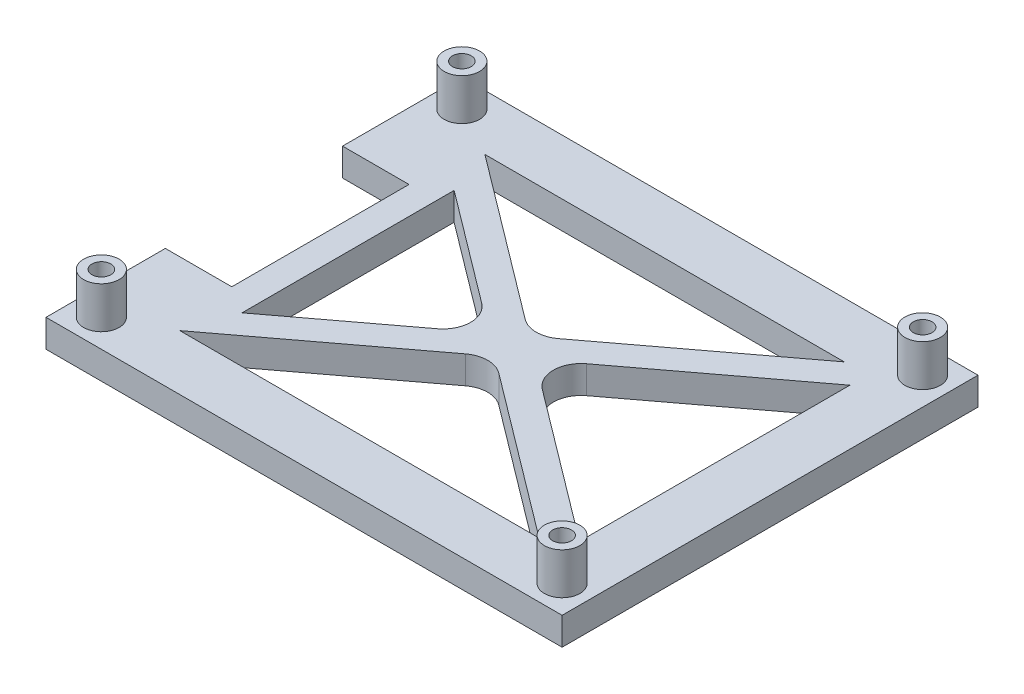
SolidWorks part; units mm, degrees
ref_plane "Front Plane" through (0, 0, 0) normal (0, 0, 1) x (1, 0, 0)
ref_plane "Top Plane" through (0, 0, 0) normal (0, 1, 0) x (1, 0, 0)
ref_plane "Right Plane" through (0, 0, 0) normal (1, 0, 0) x (0, 0, -1)
sketch "Sketch2" plane through (0, 0, 0) normal (0, 1, 0) x (1, 0, 0)
  line L0 (-36.6, -24.4209) -> (-36.6, 24.4209)
  line L1 (41.6, -32.55) -> (-41.6, -32.55) construction
  line L2 (41.6, -32.55) -> (41.6, 32.55) construction
  line L3 (41.6, 32.55) -> (-41.6, 32.55) construction
  line L4 (-41.6, -32.55) -> (-41.6, 32.55) construction
  line L5 (41.6, -32.55) -> (-41.6, 32.55) construction
  line L6 (41.6, 32.55) -> (-41.6, -32.55) construction
  line L8 (36.6, -24.4209) -> (36.6, 24.4209)
  line L9 (32.443, -27.55) -> (-32.443, -27.55)
  line L10 (-46.6, -37.55) -> (-46.6, 37.55)
  line L11 (46.6, 37.55) -> (-46.6, 37.55)
  line L12 (46.6, -37.55) -> (46.6, 37.55)
  line L13 (46.6, -37.55) -> (-46.6, -37.55)
  line L14 (-36.6, -27.55) -> (36.6, 27.55) construction
  line L15 (-36.6, 27.55) -> (36.6, -27.55) construction
  line L16 (-32.443, -27.55) -> (0, -3.1291)
  line L17 (-36.6, 24.4209) -> (-4.157, 0)
  line L18 (-36.6, -24.4209) -> (-4.157, 0)
  line L19 (-32.443, 27.55) -> (0, 3.1291)
  line L20 (-38.1035, 25.5526) -> (35.0965, -29.5474) construction
  line L21 (-36.6, -27.55) -> (-36.6, 27.55) construction
  line L22 (36.6, 27.55) -> (-36.6, 27.55) construction
  line L23 (-35.0965, 29.5474) -> (38.1035, -25.5526) construction
  line L24 (-38.1035, -25.5526) -> (35.0965, 29.5474) construction
  line L25 (32.443, 27.55) -> (-32.443, 27.55)
  line L26 (36.6, -27.55) -> (36.6, 27.55) construction
  line L27 (-35.0965, -29.5474) -> (38.1035, 25.5526) construction
  line L28 (36.6, -27.55) -> (-36.6, -27.55) construction
  line L29 (-2.0785, 1.5646) -> (-2.0383, 1.5948)
  line L30 (-2.0785, -1.5646) -> (-2.0383, -1.5948)
  line L31 (0, -3.1291) -> (32.443, -27.55)
  line L32 (2.0383, -1.5948) -> (2.0785, -1.5646)
  line L33 (4.157, 0) -> (36.6, 24.4209)
  line L34 (4.157, 0) -> (36.6, -24.4209)
  line L35 (2.0383, 1.5948) -> (2.0785, 1.5646)
  line L36 (0, 3.1291) -> (32.443, 27.55)
  circle A0 centre (-41.6, 32.55) radius 1.7
  circle A1 centre (41.6, 32.55) radius 1.7
  circle A2 centre (41.6, -32.55) radius 1.7
  circle A3 centre (-41.6, -32.55) radius 1.7
  point P0 (0, 0)
  dimension "D8" = 3.4
  dimension "D1" = 83.2
  dimension "D2" = 65.1
  dimension "D7" = 5
  dimension "D3" = 5
  dimension "D4" = 5
  dimension "D5" = 2.5
  dimension "D6" = 2.5
extrude "Boss-Extrude2" add sketch "Sketch2" along normal blind 5
fillet "Fillet1" radius 5 4 edges at (4.157, 2.5, 0) (-4.157, 2.5, 0) (0, 2.5, -3.1291) (0, 2.5, 3.1291)
sketch "Sketch4" plane through (0, 5, 0) normal (0, 1, 0) x (1, 0, 0)
  circle A0 centre (-41.6, 32.55) radius 3.2
  circle A1 centre (-41.6, 32.55) radius 1.7 construction
  circle A2 centre (-41.6, 32.55) radius 1.7
  circle A3 centre (41.6, 32.55) radius 1.7
  circle A4 centre (41.6, 32.55) radius 3.2
  circle A5 centre (41.6, -32.55) radius 1.7
  circle A7 centre (-41.6, -32.55) radius 1.7
  circle A8 centre (-41.6, -32.55) radius 3.2
  circle A9 centre (41.6, -32.55) radius 3.2
  dimension "D1" = 1.5
extrude "Boss-Extrude3" add sketch "Sketch4" along normal blind 7.5
sketch "Sketch6" plane through (0, 5, 0) normal (0, 1, 0) x (1, 0, 0)
  line L0 (-46.6, -37.55) -> (-46.6, 37.55) construction
  line L1 (-46.6, -16) -> (-36.6, -16)
  line L2 (-46.6, -16) -> (-46.6, 16)
  line L3 (-46.6, 16) -> (-36.6, 16)
  line L4 (-36.6, -16) -> (-36.6, 16)
  line L5 (-36.6, -24.4209) -> (-36.6, 24.4209) construction
  point P8 (-36.6, 0)
  dimension "D1" = 32
extrude "Cut-Extrude1" cut sketch "Sketch6" against normal through all
sketch "Sketch7" plane through (0, 5, 0) normal (0, 1, 0) x (1, 0, 0)
  line L0 (-36.6, 16) -> (-34.6, 16)
  line L1 (-34.6, 16) -> (-34.6, -16)
  line L2 (-34.6, -16) -> (-36.6, -16)
  line L3 (-36.6, -16) -> (-36.6, -24.4209)
  line L4 (-36.6, -24.4209) -> (-29.6, -19.1518)
  line L5 (-36.6, -24.4209) -> (-9.464, -3.9948) construction
  line L6 (-29.6, -19.1518) -> (-29.6, 19.1518)
  line L7 (-36.6, 24.4209) -> (-9.464, 3.9948) construction
  line L8 (-29.6, 19.1518) -> (-36.6, 24.4209)
  line L9 (-36.6, 24.4209) -> (-36.6, 16)
  dimension "D1" = 12
  dimension "D2" = 5
extrude "Boss-Extrude4" add sketch "Sketch7" against normal up to surface (5 mm away) up to face at (-41.6, 0, 34.25)
